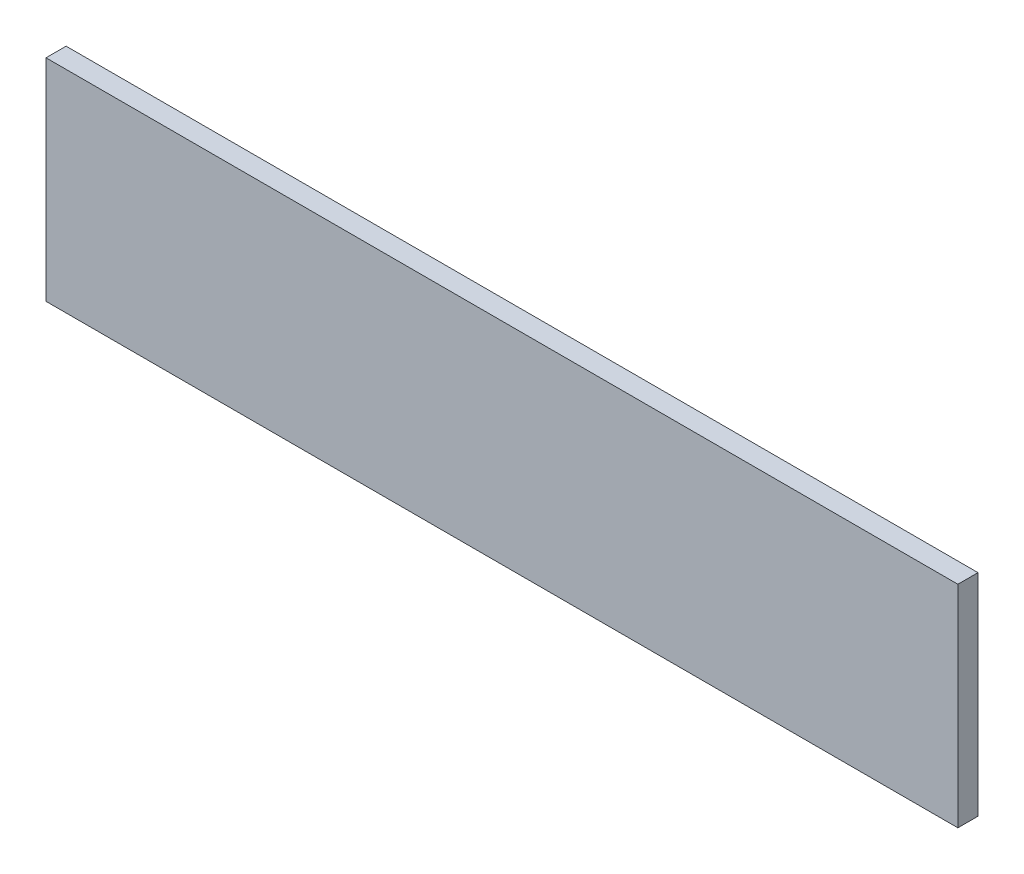
SolidWorks part; units mm, degrees
ref_plane "Front Plane" through (0, 0, 0) normal (0, 0, 1) x (1, 0, 0)
ref_plane "Top Plane" through (0, 0, 0) normal (0, 1, 0) x (1, 0, 0)
ref_plane "Right Plane" through (0, 0, 0) normal (1, 0, 0) x (0, 0, -1)
sketch "Sketch1" plane through (0, 0, 0) normal (1, 0, 0) x (0, 0, -1)
  line L0 (3.06, 32.08) -> (3.06, 0)
  line L1 (3.06, 32.08) -> (0, 32.08)
  line L2 (3.06, 0) -> (0, 0)
  line L3 (0, 32.08) -> (0, 0)
  dimension "D1" = 32.08
  dimension "D2" = 3.06
extrude "Boss-Extrude1" add sketch "Sketch1" along normal blind 138.67
